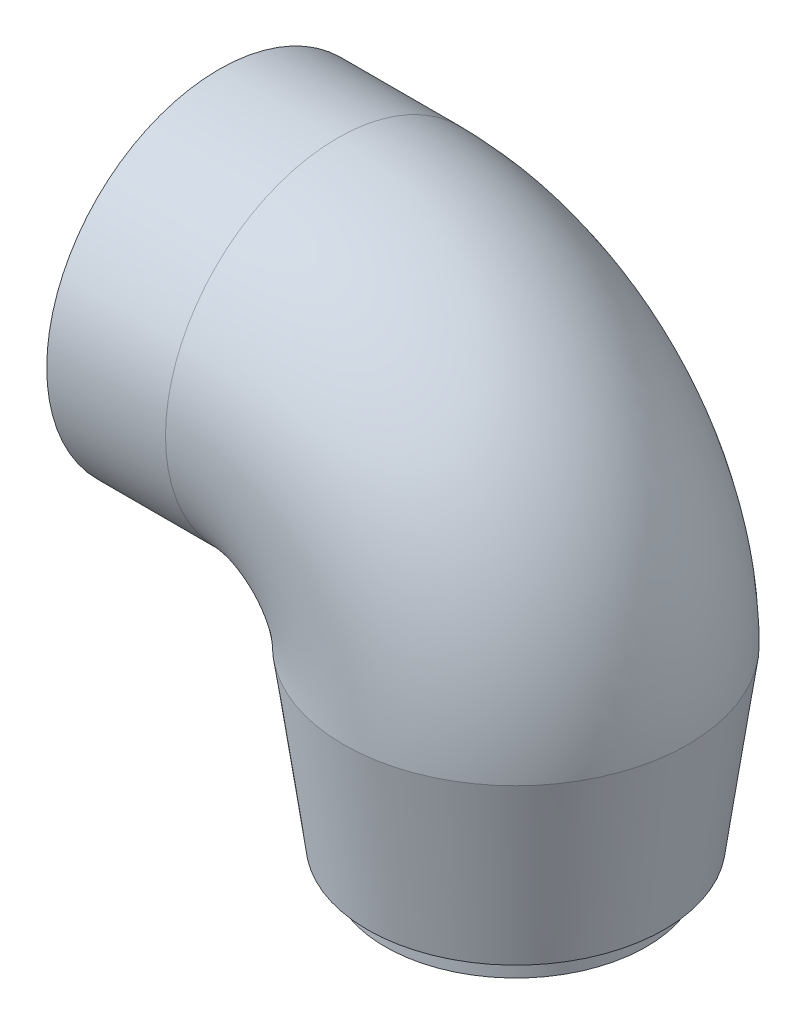
SolidWorks part; units mm, degrees
ref_plane "Front Plane" through (0, 0, 0) normal (0, 0, 1) x (1, 0, 0)
ref_plane "Top Plane" through (0, 0, 0) normal (0, 1, 0) x (1, 0, 0)
ref_plane "Right Plane" through (0, 0, 0) normal (1, 0, 0) x (0, 0, -1)
sketch "Sketch1" plane through (0, 0, 0) normal (0, 0, 1) x (1, 0, 0)
  line L0 (0, 30) -> (-20, 30)
  line L1 (30, 0) -> (30, -33)
  arc A0 (30, 0) -> (0, 30) centre (0, 0) ccw
  dimension "D1" = 30
  dimension "D2" = 20
  dimension "D3" = 33
ref_plane "Plane1" through (0, -33, 0) normal (0, 1, 0) x (1, 0, 0)
sketch "Sketch2" plane through (0, -33, 0) normal (0, 1, 0) x (1, 0, 0)
  circle A0 centre (30, 0) radius 29
  circle A1 centre (30, 0) radius 25
  dimension "D1" = 58
  dimension "D2" = 50
sweep "Sweep1" add profiles "Sketch2" path "Sketch1"
sketch "Sketch3" plane through (-20, 0, 0) normal (-1, 0, 0) x (0, 0, 1)
  circle A0 centre (0, 30) radius 27
  circle A1 centre (0, 30) radius 25
  dimension "D1" = 54
  dimension "D2" = 50
extrude "Cut-Extrude1" cut sketch "Sketch3" against normal blind 7
ref_plane "Plane2" through (30, 0, 0) normal (1, 0, 0) x (0, 0, -1)
sketch "Sketch7" plane through (30, 0, 0) normal (1, 0, 0) x (0, 0, -1)
  line L0 (25, 0) -> (20, -33)
  line L1 (-29, 0) -> (29, 0) construction
  line L2 (31.9, -33) -> (-31.9, -33) construction
  line L3 (20, -33) -> (25, -33)
  line L4 (25, -33) -> (25, 0)
  line L5 (29, -33) -> (29, 0) construction
  line L6 (0, 0) -> (0, -33) construction
  dimension "D1" = 4
  dimension "D2" = 5
revolve "Revolve2" add sketch "Sketch7" angle 360 about L6
sketch "Sketch8" plane through (0, -33, 0) normal (0, -1, 0) x (1, 0, 0)
  circle A0 centre (30, 0) radius 22
  circle A1 centre (30, 0) radius 29
  dimension "D1" = 58
  dimension "D2" = 44
extrude "Cut-Extrude3" cut sketch "Sketch8" against normal blind 4
sketch "Sketch10" plane through (30, 0, 0) normal (1, 0, 0) x (0, 0, -1)
  line L0 (29, 0) -> (25, -29)
  line L2 (25, -29) -> (29, -29)
  line L3 (29, -29) -> (29, 0)
  line L4 (0, 0) -> (0, -23) construction
  line L5 (0, 0) -> (0, -29) construction
  line L6 (-29, -29) -> (29, -29) construction
  dimension "D1" = 4
revolve "Cut-Revolve2" cut sketch "Sketch10" angle 360 about L4
